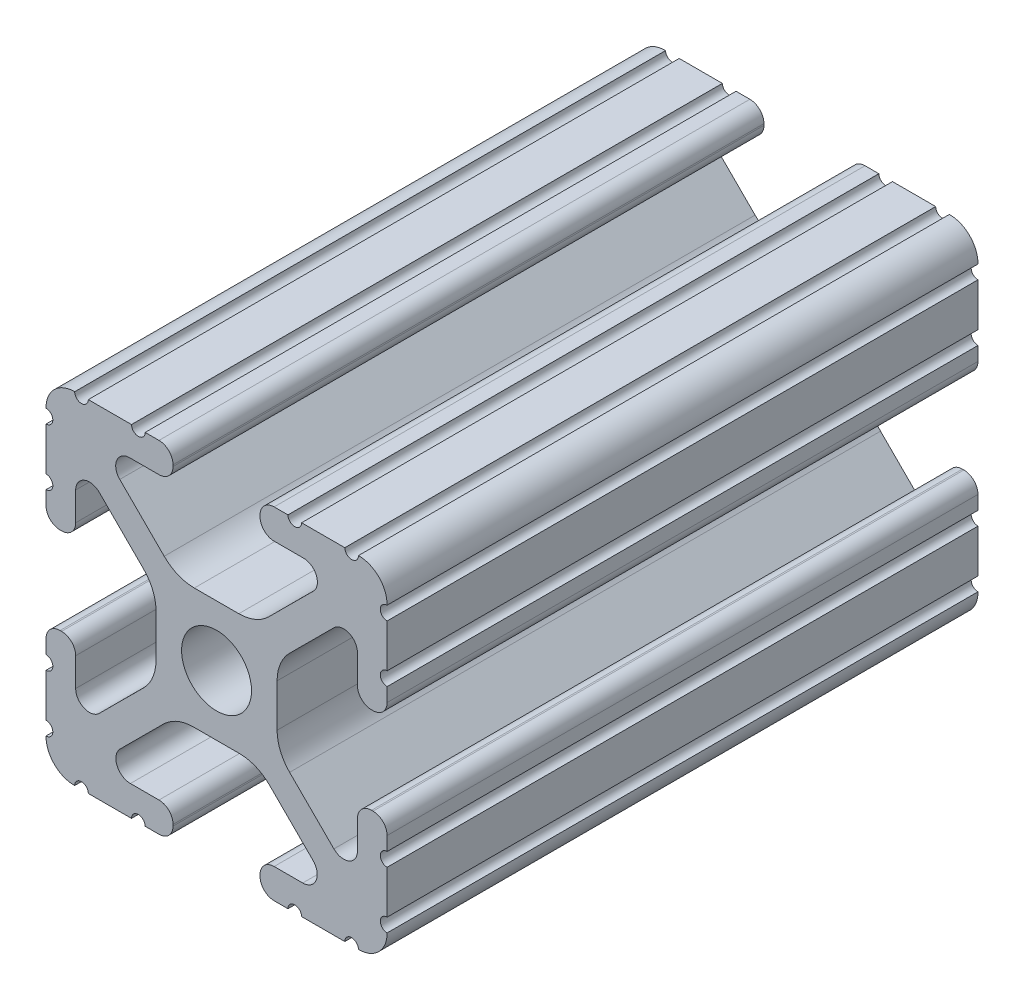
SolidWorks part; units mm, degrees
ref_plane "Front Plane" through (0, 0, 0) normal (0, 0, 1) x (1, 0, 0)
ref_plane "Top Plane" through (0, 0, 0) normal (0, 1, 0) x (1, 0, 0)
ref_plane "Right Plane" through (0, 0, 0) normal (1, 0, 0) x (0, 0, -1)
sketch "Sketch1" plane through (0, 0, 0) normal (0, 0, 1) x (1, 0, 0)
  line L88 (-7.1797, -8.6452) -> (-3.9523, -5.4237)
  line L89 (-1.7093, -4.4958) -> (1.7093, -4.4958)
  line L90 (3.9523, -5.4237) -> (7.1797, -8.6452)
  line L91 (6.4164, -10.4902) -> (4.2875, -10.4902)
  line L92 (3.2385, -11.5392) -> (3.2385, -11.651)
  line L93 (4.2875, -12.7) -> (5.3171, -12.7)
  line L94 (6.3331, -12.7) -> (9.5504, -12.7)
  line L95 (12.7, -9.5504) -> (12.7, -6.3331)
  line L96 (12.7, -5.3171) -> (12.7, -4.2875)
  line L97 (11.651, -3.2385) -> (11.5392, -3.2385)
  line L98 (10.4902, -4.2875) -> (10.4902, -6.4021)
  line L99 (8.7371, -7.1294) -> (5.441, -3.8408)
  line L100 (4.5085, -1.5932) -> (4.5085, 1.5932)
  line L101 (5.441, 3.8408) -> (8.7371, 7.1294)
  line L102 (10.4902, 6.4021) -> (10.4902, 4.2875)
  line L103 (11.5392, 3.2385) -> (11.651, 3.2385)
  line L104 (12.7, 4.2875) -> (12.7, 5.3171)
  line L105 (12.7, 6.3331) -> (12.7, 9.5504)
  line L106 (9.5504, 12.7) -> (6.3331, 12.7)
  line L107 (5.3171, 12.7) -> (4.2875, 12.7)
  line L108 (3.2385, 11.651) -> (3.2385, 11.5392)
  line L109 (4.2875, 10.4902) -> (6.4768, 10.4902)
  line L110 (7.207, 8.7244) -> (3.8983, 5.4232)
  line L111 (1.6558, 4.4958) -> (-1.6558, 4.4958)
  line L112 (-3.8983, 5.4232) -> (-7.207, 8.7244)
  line L113 (-6.4768, 10.4902) -> (-4.2875, 10.4902)
  line L114 (-3.2385, 11.5392) -> (-3.2385, 11.651)
  line L115 (-4.2875, 12.7) -> (-5.3171, 12.7)
  line L116 (-6.3331, 12.7) -> (-9.5504, 12.7)
  line L117 (-12.7, 9.5504) -> (-12.7, 6.3331)
  line L118 (-12.7, 5.3171) -> (-12.7, 4.2875)
  line L119 (-11.651, 3.2385) -> (-11.5392, 3.2385)
  line L120 (-10.4902, 4.2875) -> (-10.4902, 6.4021)
  line L121 (-8.7371, 7.1294) -> (-5.441, 3.8408)
  line L122 (-4.5085, 1.5932) -> (-4.5085, -1.5932)
  line L123 (-5.441, -3.8408) -> (-8.7371, -7.1294)
  line L124 (-10.4902, -6.4021) -> (-10.4902, -4.2875)
  line L125 (-11.5392, -3.2385) -> (-11.651, -3.2385)
  line L126 (-12.7, -4.2875) -> (-12.7, -5.3171)
  line L127 (-12.7, -6.3331) -> (-12.7, -9.5504)
  line L128 (-9.5504, -12.7) -> (-6.3331, -12.7)
  line L129 (-5.3171, -12.7) -> (-4.2875, -12.7)
  line L130 (-3.2385, -11.651) -> (-3.2385, -11.5392)
  line L131 (-4.2875, -10.4902) -> (-6.4164, -10.4902)
  circle A1 centre (0, 0) radius 2.6035
  arc A104 (-7.1797, -8.6452) -> (-6.4164, -10.4902) centre (-6.4164, -9.4098) ccw
  arc A105 (-1.7093, -4.4958) -> (-3.9523, -5.4237) centre (-1.7093, -7.6708) ccw
  arc A106 (3.9523, -5.4237) -> (1.7093, -4.4958) centre (1.7093, -7.6708) ccw
  arc A107 (6.4164, -10.4902) -> (7.1797, -8.6452) centre (6.4164, -9.4098) ccw
  arc A108 (4.2875, -10.4902) -> (3.2385, -11.5392) centre (4.2875, -11.5392) ccw
  arc A109 (3.2385, -11.651) -> (4.2875, -12.7) centre (4.2875, -11.651) ccw
  arc A110 (6.3331, -12.7) -> (5.3171, -12.7) centre (5.8251, -12.7) ccw
  arc A111 (10.5664, -12.6998) -> (9.5504, -12.7) centre (10.0584, -12.7) ccw
  arc A112 (10.5664, -12.6998) -> (12.6998, -10.5664) centre (10.5918, -10.5918) ccw
  arc A113 (12.7, -9.5504) -> (12.6998, -10.5664) centre (12.7, -10.0584) ccw
  arc A114 (12.7, -5.3171) -> (12.7, -6.3331) centre (12.7, -5.8251) ccw
  arc A115 (12.7, -4.2875) -> (11.651, -3.2385) centre (11.651, -4.2875) ccw
  arc A116 (11.5392, -3.2385) -> (10.4902, -4.2875) centre (11.5392, -4.2875) ccw
  arc A117 (8.7371, -7.1294) -> (10.4902, -6.4021) centre (9.4628, -6.4021) ccw
  arc A118 (4.5085, -1.5932) -> (5.441, -3.8408) centre (7.6835, -1.5932) ccw
  arc A119 (5.441, 3.8408) -> (4.5085, 1.5932) centre (7.6835, 1.5932) ccw
  arc A120 (10.4902, 6.4021) -> (8.7371, 7.1294) centre (9.4628, 6.4021) ccw
  arc A121 (10.4902, 4.2875) -> (11.5392, 3.2385) centre (11.5392, 4.2875) ccw
  arc A122 (11.651, 3.2385) -> (12.7, 4.2875) centre (11.651, 4.2875) ccw
  arc A123 (12.7, 6.3331) -> (12.7, 5.3171) centre (12.7, 5.8251) ccw
  arc A124 (12.6998, 10.5664) -> (12.7, 9.5504) centre (12.7, 10.0584) ccw
  arc A125 (12.6998, 10.5664) -> (10.5664, 12.6998) centre (10.5918, 10.5918) ccw
  arc A126 (9.5504, 12.7) -> (10.5664, 12.6998) centre (10.0584, 12.7) ccw
  arc A127 (5.3171, 12.7) -> (6.3331, 12.7) centre (5.8251, 12.7) ccw
  arc A128 (4.2875, 12.7) -> (3.2385, 11.651) centre (4.2875, 11.651) ccw
  arc A129 (3.2385, 11.5392) -> (4.2875, 10.4902) centre (4.2875, 11.5392) ccw
  arc A130 (7.207, 8.7244) -> (6.4768, 10.4902) centre (6.4768, 9.4563) ccw
  arc A131 (1.6558, 4.4958) -> (3.8983, 5.4232) centre (1.6558, 7.6708) ccw
  arc A132 (-3.8983, 5.4232) -> (-1.6558, 4.4958) centre (-1.6558, 7.6708) ccw
  arc A133 (-6.4768, 10.4902) -> (-7.207, 8.7244) centre (-6.4768, 9.4563) ccw
  arc A134 (-4.2875, 10.4902) -> (-3.2385, 11.5392) centre (-4.2875, 11.5392) ccw
  arc A135 (-3.2385, 11.651) -> (-4.2875, 12.7) centre (-4.2875, 11.651) ccw
  arc A136 (-6.3331, 12.7) -> (-5.3171, 12.7) centre (-5.8251, 12.7) ccw
  arc A137 (-10.5664, 12.6998) -> (-9.5504, 12.7) centre (-10.0584, 12.7) ccw
  arc A138 (-10.5664, 12.6998) -> (-12.6998, 10.5664) centre (-10.5918, 10.5918) ccw
  arc A139 (-12.7, 9.5504) -> (-12.6998, 10.5664) centre (-12.7, 10.0584) ccw
  arc A140 (-12.7, 5.3171) -> (-12.7, 6.3331) centre (-12.7, 5.8251) ccw
  arc A141 (-12.7, 4.2875) -> (-11.651, 3.2385) centre (-11.651, 4.2875) ccw
  arc A142 (-11.5392, 3.2385) -> (-10.4902, 4.2875) centre (-11.5392, 4.2875) ccw
  arc A143 (-8.7371, 7.1294) -> (-10.4902, 6.4021) centre (-9.4628, 6.4021) ccw
  arc A144 (-4.5085, 1.5932) -> (-5.441, 3.8408) centre (-7.6835, 1.5932) ccw
  arc A145 (-5.441, -3.8408) -> (-4.5085, -1.5932) centre (-7.6835, -1.5932) ccw
  arc A146 (-10.4902, -6.4021) -> (-8.7371, -7.1294) centre (-9.4628, -6.4021) ccw
  arc A147 (-10.4902, -4.2875) -> (-11.5392, -3.2385) centre (-11.5392, -4.2875) ccw
  arc A148 (-11.651, -3.2385) -> (-12.7, -4.2875) centre (-11.651, -4.2875) ccw
  arc A149 (-12.7, -6.3331) -> (-12.7, -5.3171) centre (-12.7, -5.8251) ccw
  arc A150 (-12.6998, -10.5664) -> (-12.7, -9.5504) centre (-12.7, -10.0584) ccw
  arc A151 (-12.6998, -10.5664) -> (-10.5664, -12.6998) centre (-10.5918, -10.5918) ccw
  arc A152 (-9.5504, -12.7) -> (-10.5664, -12.6998) centre (-10.0584, -12.7) ccw
  arc A153 (-5.3171, -12.7) -> (-6.3331, -12.7) centre (-5.8251, -12.7) ccw
  arc A154 (-4.2875, -12.7) -> (-3.2385, -11.651) centre (-4.2875, -11.651) ccw
  arc A155 (-3.2385, -11.5392) -> (-4.2875, -10.4902) centre (-4.2875, -11.5392) ccw
extrude "Boss-Extrude1" add sketch "Sketch1" along normal mid plane 44
